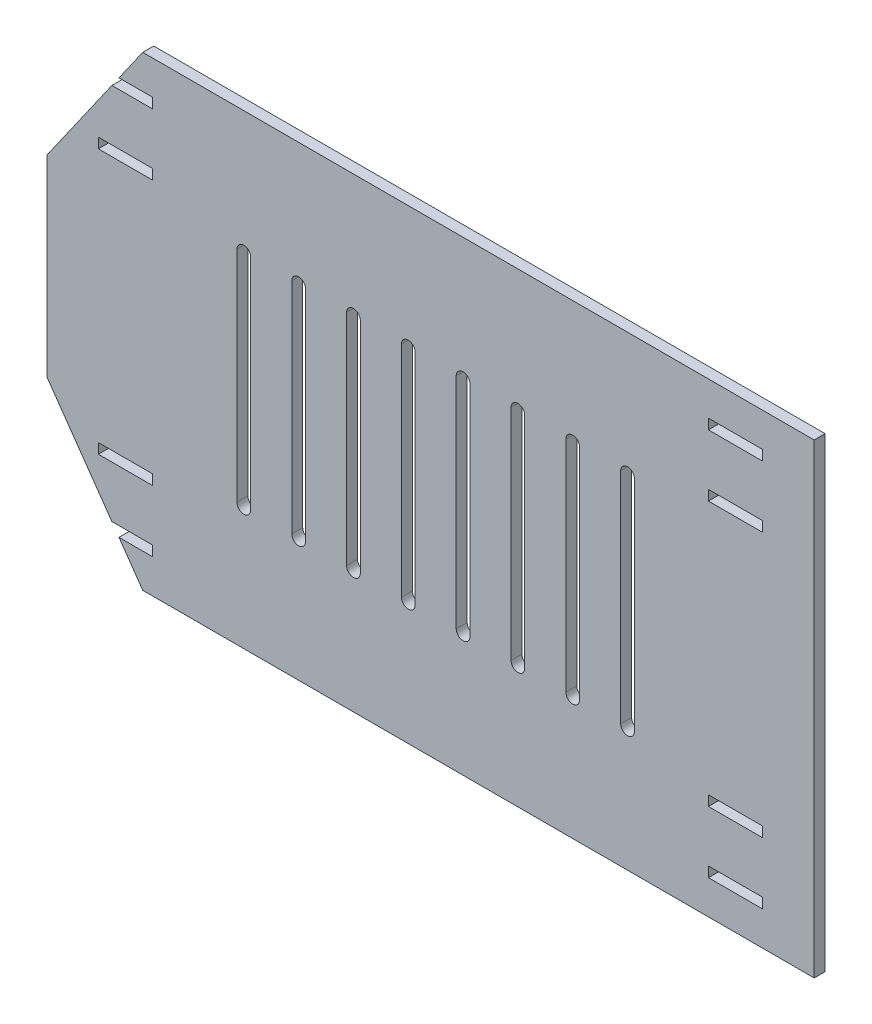
SolidWorks part; units mm, degrees
ref_plane "Ebene vorne" through (0, 0, 0) normal (0, 0, 1) x (1, 0, 0)
ref_plane "Ebene oben" through (0, 0, 0) normal (0, 1, 0) x (1, 0, 0)
ref_plane "Ebene rechts" through (0, 0, 0) normal (1, 0, 0) x (0, 0, -1)
sketch "Skizze1" plane through (0, 0, 0) normal (0, 0, 1) x (1, 0, 0)
  line L0 (35.0104, 0) -> (0, 50)
  line L1 (35.0104, 0) -> (280, 0)
  line L2 (0, 50) -> (0, 120)
  line L3 (35.0104, 170) -> (280, 170)
  line L4 (280, 0) -> (280, 170)
  line L5 (-218.8188, 85) -> (339.1358, 85) construction
  line L6 (35.0104, 170) -> (0, 120)
  line L7 (-22.3061, 135) -> (135.2106, 135) construction
  line L16 (140, 208.4543) -> (140, -82.6571) construction
  line L17 (70, 192.4344) -> (70, 92.8351) construction
  dimension "D1" = 55
  dimension "D2" = 170
  dimension "D3" = 50
  dimension "D4" = 50
  dimension "D8" = 280
  dimension "D9" = 70
extrude "Aufsatz-Linear austragen1" add sketch "Skizze1" along normal blind 4 contours L6 L2 L0 L1 L4 L3
ref_plane "Ebene1" through (0, 85, 0) normal (0, 1, 0) x (1, 0, 0)
ref_plane "Ebene2" through (140, 0, 0) normal (-1, 0, 0) x (0, 0, 1)
sketch "Skizze2" plane through (0, 0, 4) normal (0, 0, 1) x (1, 0, 0)
  line L0 (18.8, 157.6) -> (38.6, 157.6)
  line L1 (18.8, 157.6) -> (18.8, 153.9)
  line L2 (18.8, 153.9) -> (38.6, 153.9)
  line L3 (38.6, 157.6) -> (38.6, 153.9)
  line L4 (18.8, 135.1) -> (38.6, 135.1)
  line L5 (18.8, 135.1) -> (18.8, 131.4)
  line L6 (18.8, 131.4) -> (38.6, 131.4)
  line L7 (38.6, 135.1) -> (38.6, 131.4)
  line L8 (28.7, 189.0097) -> (28.7, 47.8067) construction
  line L9 (-7.6278, 144.5) -> (120.9906, 144.5) construction
  line L12 (38.7, 157.9) -> (38.7, 153.9) construction
  line L13 (18.7, 153.9) -> (18.7, 157.9) construction
  line L14 (20.679, 153.9) -> (36.7, 153.9) construction
  line L15 (36.7, 135.1) -> (20.679, 135.1) construction
  dimension "D1" = 18.8
  dimension "D2" = 3.7
  dimension "D3" = 19.8
extrude "Schnitt-Linear austragen1" cut sketch "Skizze2" against normal up to next (4 mm away)
mirror "Spiegeln1" about plane through (0, 85, 0) normal (0, 1, 0) of "Schnitt-Linear austragen1"
mirror "Spiegeln2" about plane through (140, 0, 0) normal (-1, 0, 0) of "Spiegeln1", "Schnitt-Linear austragen1"
sketch "Skizze4" plane through (0, 0, 4) normal (0, 0, 1) x (1, 0, 0)
  line L0 (2.2, 85) -> (-2.2, 85) construction
  line L1 (69.3754, 85) -> (74.3754, 85)
  line L2 (69.3754, 85) -> (69.3754, 125)
  line L4 (74.3754, 85) -> (74.3754, 125)
  arc A0 (69.3754, 125) -> (74.3754, 125) centre (71.8754, 125) cw
  point P7 (0, 0)
  dimension "D1" = 5
  dimension "D2" = 40
extrude "Schnitt-Linear austragen2" cut sketch "Skizze4" against normal up to next (4 mm away)
mirror "Spiegeln3" about plane through (0, 85, 0) normal (0, 1, 0) of "Schnitt-Linear austragen2"
pattern_linear "Lineares Muster1" count 8 spacing 20 along (1, 0, 0) of "Spiegeln3", "Schnitt-Linear austragen2"
